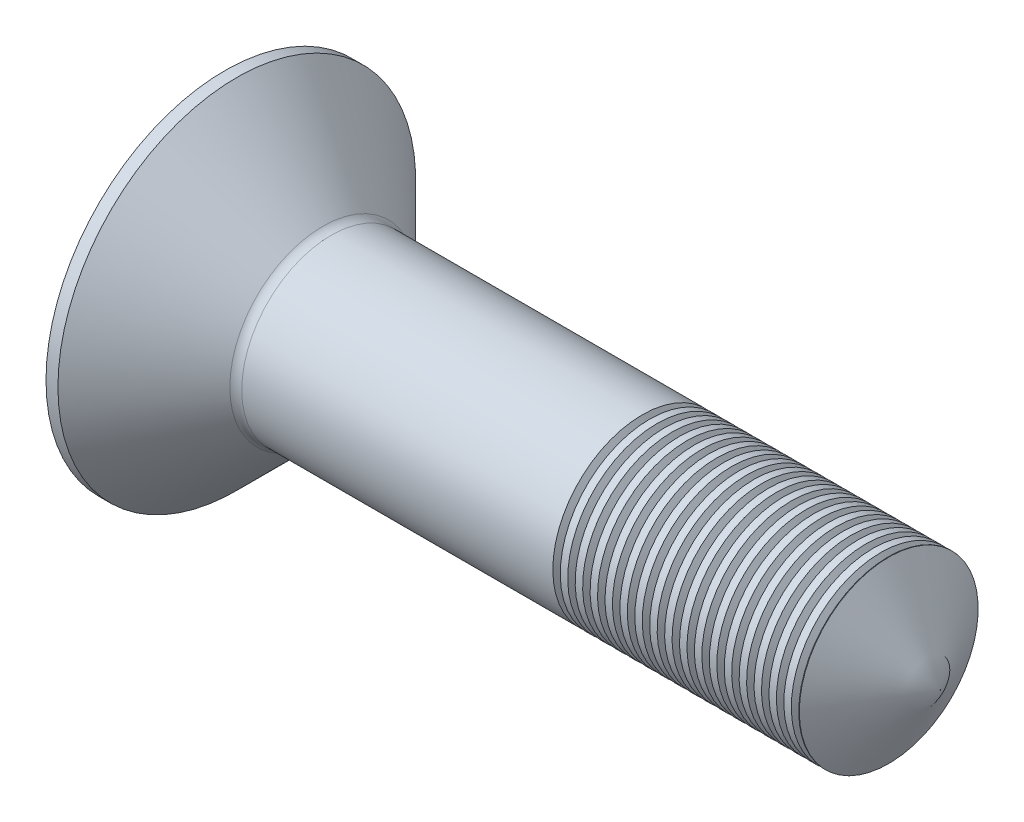
SolidWorks part; units mm, degrees
ref_plane "Front" through (0, 0, 0) normal (0, 0, 1) x (1, 0, 0)
ref_plane "Top" through (0, 0, 0) normal (0, 1, 0) x (1, 0, 0)
ref_plane "Right" through (0, 0, 0) normal (1, 0, 0) x (0, 0, -1)
sketch "Sketch1" plane through (0, 0, 0) normal (0, 1, 0) x (1, 0, 0)
  line L0 (-6.5065, 0) -> (5.6973, 0) construction
  line L1 (1.7, 1.5) -> (12, 1.5)
  line L2 (1.7, 1.5) -> (0.2, 3)
  line L3 (0.2, 3) -> (0, 3)
  line L4 (0, 3) -> (0, 0)
  line L5 (12, 1.5) -> (12, 0)
  line L6 (12, 0) -> (0, 0)
  dimension "D1" = 45
  dimension "d" = 3
  dimension "dk" = 6
  dimension "l" = 12
  dimension "k" = 1.7
revolve "Base" add sketch "Sketch1" angle 360 about L0
cosmetic thread "ThreadCosmetic1"
sketch "Sketch3" plane through (0, 0, 0) normal (0, 0, 1) x (1, 0, 0)
  line L0 (4.8835, 0) -> (6.2249, 0) construction
  line L2 (12.1576, 0) -> (12.1576, 20)
  line L3 (12.1576, 20) -> (0.453, 20)
  line L4 (0.453, 20) -> (12, 0)
  line L5 (12, 0) -> (12.1576, 0)
  line L7 (12, -1.5) -> (12, 1.5) construction
  dimension "D1" = 60
  dimension "D2" = 20
  dimension "D3" = 0.1576
revolve "Cut-Revolve1" cut sketch "Sketch3" angle 360 about L0
fillet "Fillet2" radius 0.2 1 edges at (1.7, 0, 1.5)
ref_plane "Plane1" through (1.95, 0, 0) normal (-1, 0, 0) x (0, 0, 1)
sketch "Sketch2" plane through (0, -0.6808, 0.3068) normal (-1, 0, 0) x (0, 0, 1)
  line L0 (-2.7047, 0.6808) -> (2.0912, 0.6808) construction
  line L1 (-0.3068, 2.3397) -> (-0.3068, -2.278) construction
  line L2 (-0.6868, 1.0608) -> (-2.2068, 1.0608)
  line L3 (0.0732, -1.2192) -> (-0.6868, -1.2192)
  line L4 (0.0732, -1.2192) -> (0.0732, 0.3008)
  line L5 (0.0732, 2.5808) -> (-0.6868, 2.5808)
  line L6 (-0.6868, -1.2192) -> (-0.6868, 0.3008)
  line L7 (1.5932, 1.0608) -> (0.0732, 1.0608)
  line L8 (1.5932, 1.0608) -> (1.5932, 0.3008)
  line L9 (1.5932, 0.3008) -> (0.0732, 0.3008)
  line L10 (-2.2068, 1.0608) -> (-2.2068, 0.3008)
  line L11 (-0.6868, 0.3008) -> (-2.2068, 0.3008)
  line L12 (-0.6868, 1.0608) -> (-0.6868, 2.5808)
  line L13 (0.0732, 1.0608) -> (0.0732, 2.5808)
  point P19 (-0.6868, 1.0608)
  point P24 (0.0732, 1.0608)
  dimension "D1" = 0.76
  dimension "m" = 3.8
  dimension "D2" = 3.8
  dimension "D3" = 0.76
sketch "Sketch4" plane through (1.95, 0, 0) normal (-1, 0, 0) x (0, 0, 1)
  point P0 (0, 0)
loft "Cut-Loft1" cut profiles "Sketch2", "Sketch4"
sketch "Sketch5" plane through (0, 0, 0) normal (0, 0, 1) x (1, 0, 0)
  line L0 (7, 1.7) -> (7.125, 1.7)
  line L1 (7.125, 1.7) -> (7.125, 1.5)
  line L2 (7.125, 1.5) -> (7.0625, 1.3917)
  line L3 (7, 1.5) -> (7.0625, 1.3917)
  line L4 (7, 1.7) -> (7, 1.5)
  line L5 (10.7743, 0) -> (0, 0) construction
  line L6 (7, 1.5) -> (7.125, 1.5) construction
  line L7 (7.0625, 1.5) -> (7.0625, 1.3917) construction
  line L8 (11.134, 1.5) -> (1.7828, 1.5) construction
  point P5 (7.0625, 1.7)
  dimension "D1" = 0.2
  dimension "D2" = 0.125
  dimension "D3" = 5
revolve "Cut-Revolve10" cut sketch "Sketch5" angle 360 about L5
pattern_linear "LPattern10" count 20 spacing 0.25 along (1, 0, 0) of "Cut-Revolve10"
equation "\"D2@Sketch2\" = \"m@Sketch2\""
equation "\"D3@Sketch2\" = \"D1@Sketch2\""
equation "\"D1@Sketch2\" = \"m@Sketch2\" / 5"
equation "\"D1@Plane1\" = \"k@Sketch1\" + 0.25"
equation "\"D2@Sketch5\" =  ( \"d@Sketch1\" - \"D2@ThreadCosmetic1\" )  / 2"
equation "\"D3@Sketch5\" = \"D1@ThreadCosmetic1\" + \"d@Sketch1\" / 2"
equation "\"D3@LPattern10\" =\"D2@Sketch5\"* 2"
equation "\"D1@LPattern10\" = \"D3@Sketch5\" / \"D3@LPattern10\""
